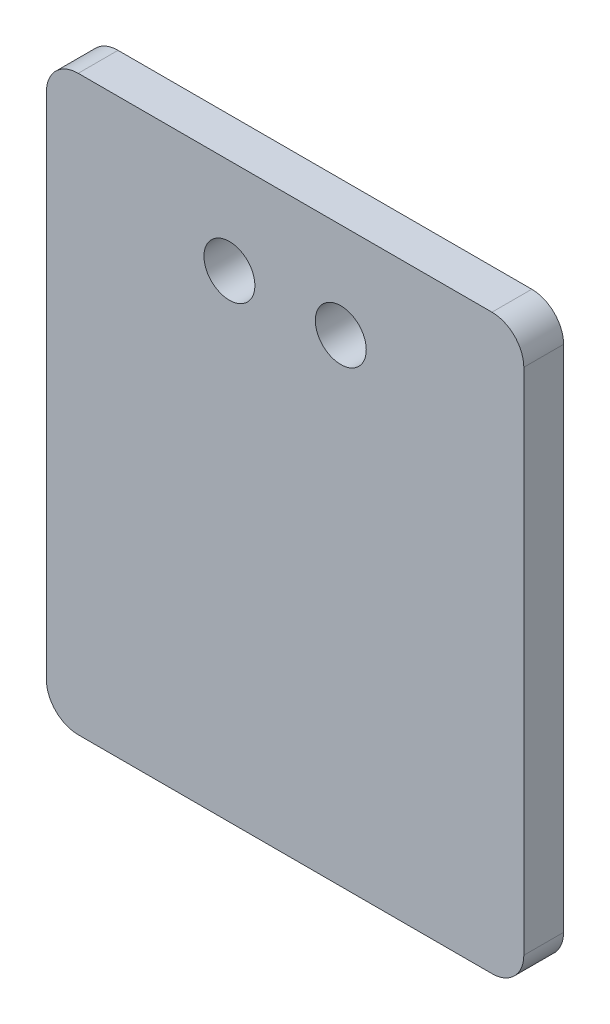
SolidWorks part; units mm, degrees
ref_plane "Front Plane" through (0, 0, 0) normal (0, 0, 1) x (1, 0, 0)
ref_plane "Top Plane" through (0, 0, 0) normal (0, 1, 0) x (1, 0, 0)
ref_plane "Right Plane" through (0, 0, 0) normal (1, 0, 0) x (0, 0, -1)
sketch "Sketch1" plane through (0, 0, 0) normal (0, 0, 1) x (1, 0, 0)
  line L0 (11.5, -6) -> (18.5, -6) construction
  line L1 (0, 0) -> (30, 0)
  line L2 (0, 0) -> (0, -36)
  line L3 (0, -36) -> (30, -36)
  line L4 (30, 0) -> (30, -36)
  line L5 (0, 0) -> (30, -36) construction
  line L6 (0, -36) -> (30, 0) construction
  circle A0 centre (11.5, -6) radius 1.6
  circle A1 centre (18.5, -6) radius 1.6
  point P4 (15, -18)
  point P10 (15, -6)
  dimension "D2" = 3.2
  dimension "D1" = 30
  dimension "D3" = 7
  dimension "D4" = 6
  dimension "D5" = 30
extrude "Boss-Extrude1" add sketch "Sketch1" along normal blind 2.5
fillet "Fillet1" radius 2 4 edges at (30, -36, 1.25) (0, -36, 1.25) (0, 0, 1.25) (30, 0, 1.25)
